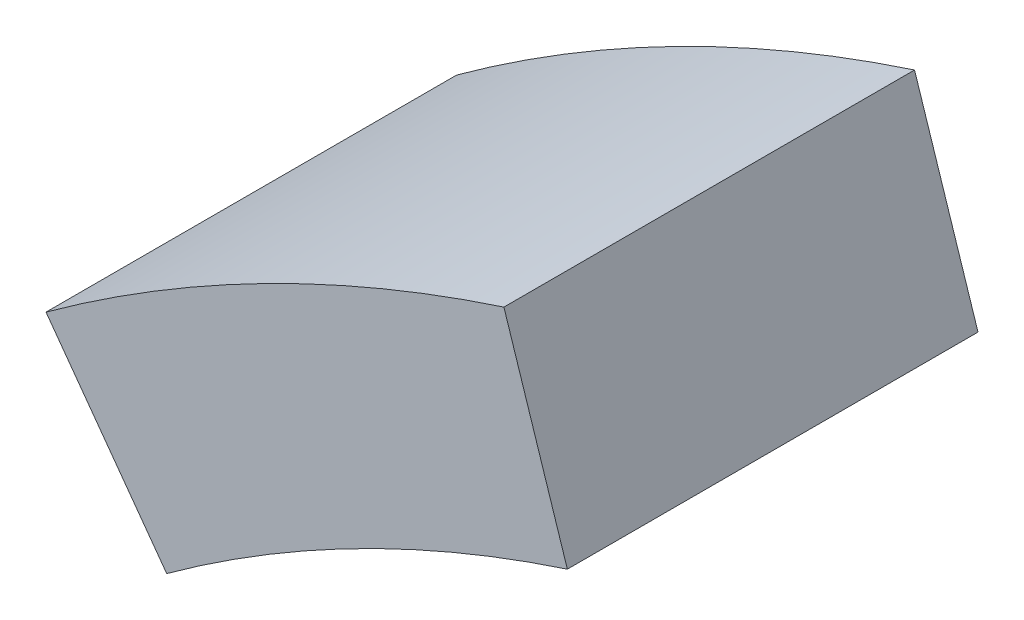
SolidWorks part; units mm, degrees
material "砖"
ref_plane "前视基准面" through (0, 0, 0) normal (0, 0, 1) x (1, 0, 0)
ref_plane "上视基准面" through (0, 0, 0) normal (0, 1, 0) x (1, 0, 0)
ref_plane "右视基准面" through (0, 0, 0) normal (1, 0, 0) x (0, 0, -1)
sketch "草图1" plane through (0, 0, 0) normal (0, 0, 1) x (1, 0, 0)
  line L0 (-4560, 0) -> (-7920, 0)
  line L1 (-12480, 7680) -> (0, 7680)
  line L2 (-12480, 7680) -> (-12480, 0)
  line L3 (-12480, 0) -> (0, 0)
  line L4 (0, 7680) -> (0, 0)
  line L5 (-7920, 0) -> (-7920, 3840)
  line L6 (-7920, 3840) -> (-4560, 3840)
  line L7 (-4560, 3840) -> (-4560, 0)
  line L8 (-7920, 3840) -> (-8160, 3840)
  line L9 (-4560, 3840) -> (-4320, 3840)
  line L10 (-7837.7749, 4359.1486) -> (-8066.0285, 4433.3126)
  line L11 (-7599.1486, 4827.4792) -> (-7793.3126, 4968.5477)
  line L12 (-7227.4792, 5199.1486) -> (-7368.5477, 5393.3126)
  line L13 (-6759.1486, 5437.7749) -> (-6833.3126, 5666.0285)
  line L14 (-6240, 5520) -> (-6240, 5760)
  line L15 (-5720.8514, 5437.7749) -> (-5646.6874, 5666.0285)
  line L16 (-5252.5208, 5199.1486) -> (-5111.4523, 5393.3126)
  line L17 (-4880.8514, 4827.4792) -> (-4686.6874, 4968.5477)
  line L18 (-4642.2251, 4359.1486) -> (-4413.9715, 4433.3126)
  line L19 (-4560, 3840) -> (-4320, 3840)
  line L20 (-4573.7633, 3298.6069) -> (-4560, 3294.1349)
  line L21 (-6833.3126, 5666.0285) -> (-6928.8298, 5960)
  line L22 (-5683.7694, 5551.9017) -> (-5551.1702, 5960)
  line L23 (-5551.1702, 5960) -> (-6928.8298, 5960)
  line L24 (-7920, 0) -> (-9123.3069, 0)
  line L25 (-8160, 0) -> (-8640, 0)
  line L26 (-8160, 0) -> (-8640, 0)
  line L27 (-8640, 3840) -> (-8160, 3840)
  line L28 (-8640, 3840) -> (-8640, 4264)
  line L29 (-7837.7749, 3320.8514) -> (-7920, 3294.1349) [skipped]
  line L30 (-7599.1486, 2852.5208) -> (-7793.3126, 2711.4523) [skipped]
  line L31 (-7227.4792, 2480.8514) -> (-7368.5477, 2286.6874) [skipped]
  line L32 (-6759.1486, 2242.2251) -> (-6833.3126, 2013.9715) [skipped]
  line L33 (-6240, 2160) -> (-6240, 1920) [skipped]
  line L34 (-5720.8514, 2242.2251) -> (-5646.6874, 2013.9715) [skipped]
  line L35 (-5252.5208, 2480.8514) -> (-5111.4523, 2286.6874) [skipped]
  line L36 (-4880.8514, 2852.5208) -> (-4686.6874, 2711.4523) [skipped]
  line L37 (-8640, 4264) -> (-8112.5982, 4264)
  line L38 (-8112.5982, 4264) -> (-8592.5982, 4264)
  line L39 (-8592.5982, 4264) -> (-8592.5982, 4688)
  line L40 (-8592.5982, 4688) -> (-7962.5841, 4688)
  line L41 (-7962.5841, 4688) -> (-8442.5841, 4688)
  line L42 (-8442.5841, 4688) -> (-8442.5841, 5112)
  line L43 (-8442.5841, 5112) -> (-7678.1989, 5112)
  line L44 (-7678.1989, 5112) -> (-8158.1989, 5112)
  line L45 (-8158.1989, 5112) -> (-8158.1989, 5536)
  line L46 (-8158.1989, 5536) -> (-7139.9911, 5536)
  line L47 (-7139.9911, 5536) -> (-7619.9911, 5536)
  line L48 (-7619.9911, 5536) -> (-7619.9911, 5960)
  line L49 (-7619.9911, 5960) -> (-6928.8298, 5960)
  arc A0 (-4560, 3840) -> (-7920, 3840) centre (-6240, 3840) ccw
  arc A1 (-4320, 3840) -> (-8160, 3840) centre (-6240, 3840) ccw
  point P7 (-6240, 0)
  point P56 (-6240, 3840)
  dimension "D5" = 3840
  dimension "D1" = 12480
  dimension "D2" = 7680
  dimension "D3" = 3360
  dimension "D4" = 3840
  dimension "D7" = 240
  dimension "D8" = 480
  dimension "D9" = 424
  dimension "D10" = 720
  dimension "D11" = 480
  dimension "D12" = 480
  dimension "D13" = 480
  dimension "D14" = 480
  dimension "D6" = 20
extrude "凸台-拉伸1" add sketch "草图1" along normal blind 480 contours L13 A1 L12 A0
scale "缩放比例1" scale about origin uniform scaling yes scale factor 1.3
